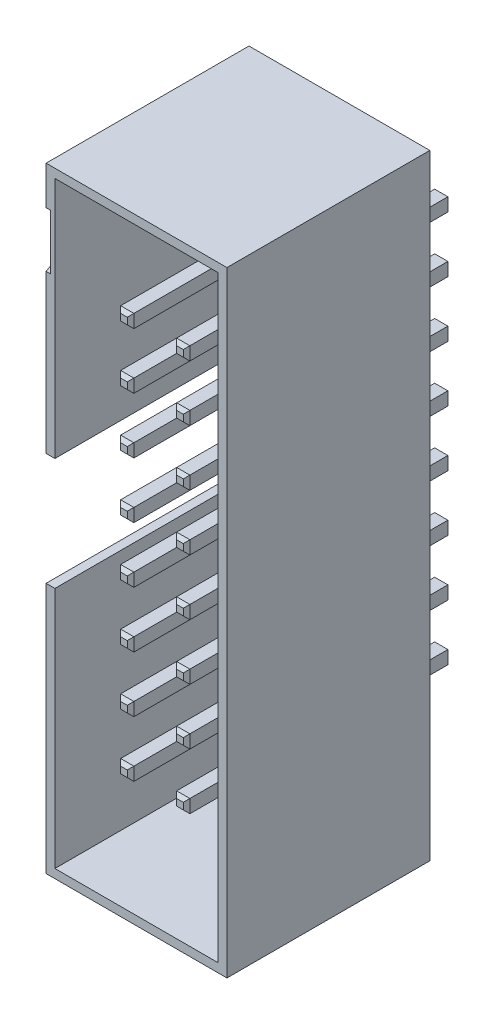
SolidWorks part; units mm, degrees
ref_plane "Plan de face" through (0, 0, 0) normal (0, 0, 1) x (1, 0, 0)
ref_plane "Plan de dessus" through (0, 0, 0) normal (0, 1, 0) x (1, 0, 0)
ref_plane "Plan de droite" through (0, 0, 0) normal (1, 0, 0) x (0, 0, -1)
sketch "Esquisse1" plane through (0, 0, 0) normal (0, 0, 1) x (1, 0, 0)
  line L1 (0, 0) -> (8.2, 0)
  line L2 (0, 0) -> (0, 27.9)
  line L3 (0, 27.9) -> (8.2, 27.9)
  line L4 (8.2, 0) -> (8.2, 27.9)
  dimension "D1" = 27.9
  dimension "D2" = 8.2
extrude "Boss.-Extru.1" add sketch "Esquisse1" along normal blind 9.2
sketch "Esquisse2" plane through (0, 0, 9.2) normal (0, 0, 1) x (1, 0, 0)
  line L0 (4.1, 13.95) -> (4.1, 27.9) construction
  line L1 (0.4, 0.4) -> (7.8, 0.4)
  line L2 (0.4, 0.4) -> (0.4, 27.5)
  line L3 (0.4, 27.5) -> (7.8, 27.5)
  line L4 (7.8, 0.4) -> (7.8, 27.5)
  line L5 (0.4, 0.4) -> (7.8, 27.5) construction
  line L6 (0.4, 27.5) -> (7.8, 0.4) construction
  line L7 (8.2, 27.9) -> (0, 27.9) construction
  line L8 (4.1, 13.95) -> (8.2, 13.95) construction
  line L9 (8.2, 0) -> (8.2, 27.9) construction
  line L10 (0, 27.9) -> (0, 0) construction
  point P0 (4.1, 13.95)
  dimension "D1" = 0.4
  dimension "D2" = 0.4
extrude "Enlèv. mat.-Extru.1" cut sketch "Esquisse2" against normal blind 8
sketch "Esquisse3" plane through (0, 0, 0) normal (0, 0, -1) x (-1, 0, 0)
  line L0 (-5.37, 22.84) -> (-8.2, 22.84) construction
  line L1 (-5.67, 23.14) -> (-5.07, 23.14)
  line L2 (-5.67, 23.14) -> (-5.67, 22.54)
  line L3 (-5.67, 22.54) -> (-5.07, 22.54)
  line L4 (-5.07, 23.14) -> (-5.07, 22.54)
  line L5 (-5.67, 23.14) -> (-5.07, 22.54) construction
  line L6 (-5.67, 22.54) -> (-5.07, 23.14) construction
  line L7 (-3.13, 23.14) -> (-2.53, 23.14)
  line L8 (-3.13, 23.14) -> (-3.13, 22.54)
  line L9 (-3.13, 22.54) -> (-2.53, 22.54)
  line L10 (-2.53, 23.14) -> (-2.53, 22.54)
  line L11 (-3.13, 23.14) -> (-2.53, 22.54) construction
  line L12 (-3.13, 22.54) -> (-2.53, 23.14) construction
  line L13 (-8.2, 0) -> (-8.2, 27.9) construction
  line L14 (-2.83, 22.84) -> (0, 22.84) construction
  line L15 (0, 27.9) -> (0, 0) construction
  line L16 (-5.37, 22.84) -> (-2.83, 22.84) construction
  line L25 (-5.67, 20.6) -> (-5.07, 20.6)
  line L26 (-5.67, 20.6) -> (-5.67, 20)
  line L27 (-5.67, 20) -> (-5.07, 20)
  line L28 (-5.07, 20.6) -> (-5.07, 20)
  line L29 (-3.13, 20.6) -> (-2.53, 20.6)
  line L30 (-3.13, 20.6) -> (-3.13, 20)
  line L31 (-3.13, 20) -> (-2.53, 20)
  line L40 (-2.53, 20.6) -> (-2.53, 20)
  line L41 (-5.37, 20.3) -> (-8.2, 20.3) construction
  line L42 (-5.67, 20.6) -> (-5.07, 20) construction
  line L43 (-5.67, 20) -> (-5.07, 20.6) construction
  line L44 (-3.13, 20.6) -> (-2.53, 20) construction
  line L45 (-3.13, 20) -> (-2.53, 20.6) construction
  line L46 (-2.83, 20.3) -> (0, 20.3) construction
  line L55 (-5.37, 20.3) -> (-2.83, 20.3) construction
  line L56 (-5.67, 18.06) -> (-5.07, 18.06)
  line L57 (-5.67, 18.06) -> (-5.67, 17.46)
  line L58 (-5.67, 17.46) -> (-5.07, 17.46)
  line L59 (-5.07, 18.06) -> (-5.07, 17.46)
  line L60 (-3.13, 18.06) -> (-2.53, 18.06)
  line L61 (-3.13, 18.06) -> (-3.13, 17.46)
  line L70 (-3.13, 17.46) -> (-2.53, 17.46)
  line L71 (-2.53, 18.06) -> (-2.53, 17.46)
  line L72 (-5.37, 17.76) -> (-8.2, 17.76) construction
  line L73 (-5.67, 18.06) -> (-5.07, 17.46) construction
  line L74 (-5.67, 17.46) -> (-5.07, 18.06) construction
  line L75 (-3.13, 18.06) -> (-2.53, 17.46) construction
  line L76 (-3.13, 17.46) -> (-2.53, 18.06) construction
  line L77 (-5.37, 5.06) -> (-5.37, 0) construction
  line L79 (0, 0) -> (-8.2, 0) construction
  line L81 (-2.83, 17.76) -> (0, 17.76) construction
  line L82 (-5.37, 17.76) -> (-2.83, 17.76) construction
  line L83 (-5.67, 15.52) -> (-5.07, 15.52)
  line L84 (-5.67, 15.52) -> (-5.67, 14.92)
  line L85 (-5.67, 14.92) -> (-5.07, 14.92)
  line L86 (-5.07, 15.52) -> (-5.07, 14.92)
  line L87 (-3.13, 15.52) -> (-2.53, 15.52)
  line L88 (-3.13, 15.52) -> (-3.13, 14.92)
  line L89 (-3.13, 14.92) -> (-2.53, 14.92)
  line L90 (-2.53, 15.52) -> (-2.53, 14.92)
  line L91 (-5.37, 15.22) -> (-8.2, 15.22) construction
  line L92 (-5.67, 15.52) -> (-5.07, 14.92) construction
  line L93 (-5.67, 14.92) -> (-5.07, 15.52) construction
  line L94 (-3.13, 15.52) -> (-2.53, 14.92) construction
  line L95 (-3.13, 14.92) -> (-2.53, 15.52) construction
  line L96 (-2.83, 15.22) -> (0, 15.22) construction
  line L97 (-5.37, 15.22) -> (-2.83, 15.22) construction
  line L98 (-5.67, 12.98) -> (-5.07, 12.98)
  line L99 (-5.67, 12.98) -> (-5.67, 12.38)
  line L100 (-5.67, 12.38) -> (-5.07, 12.38)
  line L101 (-5.07, 12.98) -> (-5.07, 12.38)
  line L102 (-3.13, 12.98) -> (-2.53, 12.98)
  line L103 (-3.13, 12.98) -> (-3.13, 12.38)
  line L104 (-3.13, 12.38) -> (-2.53, 12.38)
  line L105 (-2.53, 12.98) -> (-2.53, 12.38)
  line L106 (-5.37, 12.68) -> (-8.2, 12.68) construction
  line L107 (-5.67, 12.98) -> (-5.07, 12.38) construction
  line L108 (-5.67, 12.38) -> (-5.07, 12.98) construction
  line L109 (-3.13, 12.98) -> (-2.53, 12.38) construction
  line L110 (-3.13, 12.38) -> (-2.53, 12.98) construction
  line L111 (-2.83, 12.68) -> (0, 12.68) construction
  line L112 (-5.37, 12.68) -> (-2.83, 12.68) construction
  line L113 (-5.67, 10.44) -> (-5.07, 10.44)
  line L114 (-5.67, 10.44) -> (-5.67, 9.84)
  line L115 (-5.67, 9.84) -> (-5.07, 9.84)
  line L116 (-5.07, 10.44) -> (-5.07, 9.84)
  line L117 (-3.13, 10.44) -> (-2.53, 10.44)
  line L118 (-3.13, 10.44) -> (-3.13, 9.84)
  line L119 (-3.13, 9.84) -> (-2.53, 9.84)
  line L120 (-2.53, 10.44) -> (-2.53, 9.84)
  line L121 (-5.37, 10.14) -> (-8.2, 10.14) construction
  line L122 (-5.67, 10.44) -> (-5.07, 9.84) construction
  line L123 (-5.67, 9.84) -> (-5.07, 10.44) construction
  line L124 (-3.13, 10.44) -> (-2.53, 9.84) construction
  line L125 (-3.13, 9.84) -> (-2.53, 10.44) construction
  line L126 (-2.83, 10.14) -> (0, 10.14) construction
  line L127 (-5.37, 10.14) -> (-2.83, 10.14) construction
  line L128 (-5.67, 7.9) -> (-5.07, 7.9)
  line L129 (-5.67, 7.9) -> (-5.67, 7.3)
  line L130 (-5.67, 7.3) -> (-5.07, 7.3)
  line L131 (-5.07, 7.9) -> (-5.07, 7.3)
  line L132 (-3.13, 7.9) -> (-2.53, 7.9)
  line L133 (-3.13, 7.9) -> (-3.13, 7.3)
  line L134 (-3.13, 7.3) -> (-2.53, 7.3)
  line L135 (-2.53, 7.9) -> (-2.53, 7.3)
  line L136 (-5.37, 7.6) -> (-8.2, 7.6) construction
  line L137 (-5.67, 7.9) -> (-5.07, 7.3) construction
  line L138 (-5.67, 7.3) -> (-5.07, 7.9) construction
  line L139 (-3.13, 7.9) -> (-2.53, 7.3) construction
  line L140 (-3.13, 7.3) -> (-2.53, 7.9) construction
  line L141 (-2.83, 7.6) -> (0, 7.6) construction
  line L142 (-5.37, 7.6) -> (-2.83, 7.6) construction
  line L143 (-5.67, 5.36) -> (-5.07, 5.36)
  line L144 (-5.67, 5.36) -> (-5.67, 4.76)
  line L145 (-5.67, 4.76) -> (-5.07, 4.76)
  line L146 (-5.07, 5.36) -> (-5.07, 4.76)
  line L147 (-3.13, 5.36) -> (-2.53, 5.36)
  line L148 (-3.13, 5.36) -> (-3.13, 4.76)
  line L149 (-3.13, 4.76) -> (-2.53, 4.76)
  line L150 (-2.53, 5.36) -> (-2.53, 4.76)
  line L151 (-5.37, 5.06) -> (-8.2, 5.06) construction
  line L152 (-5.67, 5.36) -> (-5.07, 4.76) construction
  line L153 (-5.67, 4.76) -> (-5.07, 5.36) construction
  line L154 (-3.13, 5.36) -> (-2.53, 4.76) construction
  line L155 (-3.13, 4.76) -> (-2.53, 5.36) construction
  line L156 (-2.83, 5.06) -> (0, 5.06) construction
  line L157 (-5.37, 5.06) -> (-2.83, 5.06) construction
  line L158 (-5.37, 22.84) -> (-5.37, 27.9) construction
  line L159 (-8.2, 27.9) -> (0, 27.9) construction
  point P0 (-5.37, 22.84)
  point P5 (-2.83, 22.84)
  point P21 (-5.37, 20.3)
  point P26 (-2.83, 20.3)
  point P35 (-5.37, 17.76)
  point P40 (-2.83, 17.76)
  point P49 (-5.37, 15.22)
  point P54 (-2.83, 15.22)
  point P63 (-5.37, 12.68)
  point P68 (-2.83, 12.68)
  point P82 (-5.37, 10.14)
  point P87 (-2.83, 10.14)
  point P96 (-5.37, 7.6)
  point P101 (-2.83, 7.6)
  point P110 (-5.37, 5.06)
  point P115 (-2.83, 5.06)
  dimension "D1" = 2.54
  dimension "D2" = 0.6
  dimension "D4" = 2.54
  dimension "D3" = 8
extrude "Boss.-Extru.2" add sketch "Esquisse3" along normal blind 3.5 and the other way blind 8.5
chamfer "Chanfrein1" distance 0.15 angle 45 128 edges at (5.37, 12.38, 8.5) (5.37, 14.92, 8.5) (5.37, 17.46, 8.5) (5.37, 20, 8.5) (5.37, 23.14, 8.5) (5.67, 22.84, 8.5) (5.37, 22.54, 8.5) (5.07, 22.84, 8.5) (2.83, 23.14, 8.5) (3.13, 22.84, 8.5) (2.83, 22.54, 8.5) (2.53, 22.84, 8.5) (2.83, 20, 8.5) (2.83, 17.46, 8.5) (2.83, 14.92, 8.5) (2.83, 12.38, 8.5) (2.83, 12.38, -3.5) (5.37, 12.38, -3.5) (5.37, 14.92, -3.5) (2.83, 14.92, -3.5) (2.83, 17.46, -3.5) (5.37, 17.46, -3.5) (5.37, 20, -3.5) (2.83, 20, -3.5) (2.83, 22.54, -3.5) (3.13, 22.84, -3.5) (2.83, 23.14, -3.5) (2.53, 22.84, -3.5) (5.37, 22.54, -3.5) (5.67, 22.84, -3.5) (5.37, 23.14, -3.5) (5.07, 22.84, -3.5) (5.37, 12.98, 8.5) (5.67, 12.68, 8.5) (5.07, 12.68, 8.5) (5.37, 15.52, 8.5) (5.67, 15.22, 8.5) (5.07, 15.22, 8.5) (5.37, 18.06, 8.5) (5.67, 17.76, 8.5) (5.07, 17.76, 8.5) (5.37, 20.6, 8.5) (5.67, 20.3, 8.5) (5.07, 20.3, 8.5) (2.83, 20.6, 8.5) (3.13, 20.3, 8.5) (2.53, 20.3, 8.5) (2.83, 18.06, 8.5) (3.13, 17.76, 8.5) (2.53, 17.76, 8.5) (2.83, 15.52, 8.5) (3.13, 15.22, 8.5) (2.53, 15.22, 8.5) (2.83, 12.98, 8.5) (3.13, 12.68, 8.5) (2.53, 12.68, 8.5) (3.13, 12.68, -3.5) (2.83, 12.98, -3.5) (2.53, 12.68, -3.5) (5.67, 12.68, -3.5) (5.37, 12.98, -3.5) (5.07, 12.68, -3.5) (5.67, 15.22, -3.5) (5.37, 15.52, -3.5) (5.07, 15.22, -3.5) (3.13, 15.22, -3.5) (2.83, 15.52, -3.5) (2.53, 15.22, -3.5) (3.13, 17.76, -3.5) (2.83, 18.06, -3.5) (2.53, 17.76, -3.5) (5.67, 17.76, -3.5) (5.37, 18.06, -3.5) (5.07, 17.76, -3.5) (5.67, 20.3, -3.5) (5.37, 20.6, -3.5) (5.07, 20.3, -3.5) (3.13, 20.3, -3.5) (2.83, 20.6, -3.5) (2.53, 20.3, -3.5) (5.37, 9.84, -3.5) (5.67, 10.14, -3.5) (5.37, 10.44, -3.5) (5.07, 10.14, -3.5) (5.37, 7.3, -3.5) (5.67, 7.6, -3.5) (5.37, 7.9, -3.5) (5.07, 7.6, -3.5) (5.37, 4.76, -3.5) (5.67, 5.06, -3.5) (5.37, 5.36, -3.5) (5.07, 5.06, -3.5) (2.83, 4.76, -3.5) (3.13, 5.06, -3.5) (2.83, 5.36, -3.5) (2.53, 5.06, -3.5) (2.83, 7.3, -3.5) (3.13, 7.6, -3.5) (2.83, 7.9, -3.5) (2.53, 7.6, -3.5) (2.83, 9.84, -3.5) (3.13, 10.14, -3.5) (2.83, 10.44, -3.5) (2.53, 10.14, -3.5) (5.37, 5.36, 8.5) (5.67, 5.06, 8.5) (5.37, 4.76, 8.5) (5.07, 5.06, 8.5) (2.83, 5.36, 8.5) (3.13, 5.06, 8.5) (2.83, 4.76, 8.5) (2.53, 5.06, 8.5) (2.83, 7.9, 8.5) (3.13, 7.6, 8.5) (2.83, 7.3, 8.5) (2.53, 7.6, 8.5) (5.37, 7.9, 8.5) (5.67, 7.6, 8.5) (5.37, 7.3, 8.5) (5.07, 7.6, 8.5) (5.37, 10.44, 8.5) (5.67, 10.14, 8.5) (5.37, 9.84, 8.5) (5.07, 10.14, 8.5) (2.83, 10.44, 8.5) (3.13, 10.14, 8.5) (2.83, 9.84, 8.5) (2.53, 10.14, 8.5)
sketch "Esquisse4" plane through (0, 0, 9.2) normal (0, 0, 1) x (1, 0, 0)
  line L0 (0, 27.9) -> (0, 0) construction
  line L1 (0, 16.5) -> (0.4, 16.5)
  line L2 (0, 16.5) -> (0, 11.4)
  line L3 (0, 11.4) -> (0.4, 11.4)
  line L4 (0.4, 16.5) -> (0.4, 11.4)
  line L5 (0.4, 27.5) -> (0.4, 0.4) construction
  line L6 (0, 0) -> (0, 11.4) construction
  line L7 (0, 27.9) -> (0, 16.5) construction
  dimension "D1" = 5.1
extrude "Enlèv. mat.-Extru.2" cut sketch "Esquisse4" against normal up to surface (8 mm away) up to face at (2.83, 5.06, 1.2)
sketch "Esquisse5" plane through (0, 0, 0) normal (-1, 0, 0) x (0, 0, 1)
  line L0 (9.2, 26.15) -> (9.2, 23.65)
  line L1 (9.2, 27.9) -> (9.2, 16.5) construction
  line L2 (9.2, 23.65) -> (7.0349, 24.9)
  line L3 (7.0349, 24.9) -> (9.2, 26.15)
  line L4 (9.2, 27.9) -> (0, 27.9) construction
  dimension "D1" = 2.5
  dimension "D2" = 3
extrude "Enlèv. mat.-Extru.3" cut sketch "Esquisse5" against normal blind 0.2
